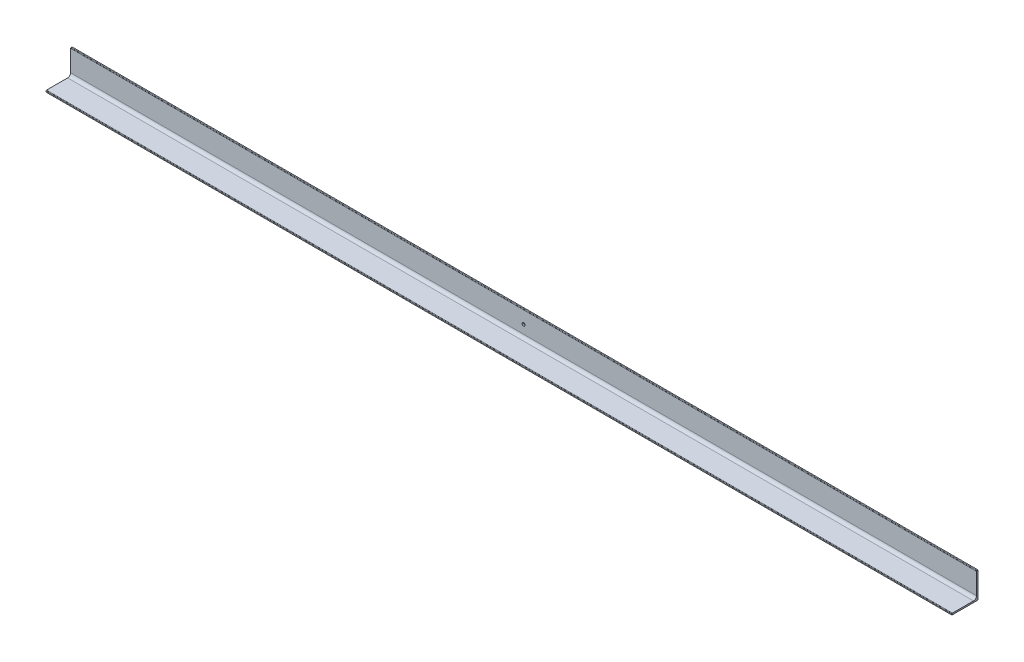
SolidWorks part; units mm, degrees
ref_plane "Front" through (0, 0, 0) normal (0, 0, 1) x (1, 0, 0)
ref_plane "Top" through (0, 0, 0) normal (0, 1, 0) x (1, 0, 0)
ref_plane "Right" through (0, 0, 0) normal (1, 0, 0) x (0, 0, -1)
sketch "Sketch1" plane through (0, 0, 0) normal (1, 0, 0) x (0, 1, 0)
  line L0 (0, 70) -> (0, 0)
  line L1 (0, 0) -> (70, 0)
  line L2 (4, 68.6667) -> (4, 12)
  line L3 (12, 4) -> (68.6667, 4)
  line L4 (0, 70) -> (2.6667, 70)
  line L5 (70, 0) -> (70, 2.6667)
  arc A0 (2.6667, 70) -> (4, 68.6667) centre (2.6667, 68.6667) cw
  arc A1 (70, 2.6667) -> (68.6667, 4) centre (68.6667, 2.6667) ccw
  arc A2 (4, 12) -> (12, 4) centre (12, 12) ccw
  dimension "r1" = 1.3333
  dimension "r" = 8
  dimension "b" = 70
  dimension "d1" = 4
  dimension "d" = 4
  dimension "b1" = 70
extrude "Base" add sketch "Sketch1" along normal mid plane 2430
sketch "草图1" plane through (0, 0, 4) normal (0, 0, 1) x (1, 0, 0)
  line L2 (0, -50) -> (0, 50) construction
  line L3 (1215, 0) -> (-1215, 0) construction
  circle A0 centre (0, 35) radius 4
  dimension "D1" = 8
  dimension "D2" = 35
extrude "切除-拉伸1" cut sketch "草图1" against normal through all
equation "\"r1@Sketch1\" = \"d@Sketch1\" / 3"
equation "\"d1@Sketch1\" = \"d@Sketch1\""
equation "\"b1@Sketch1\" = \"b@Sketch1\""
